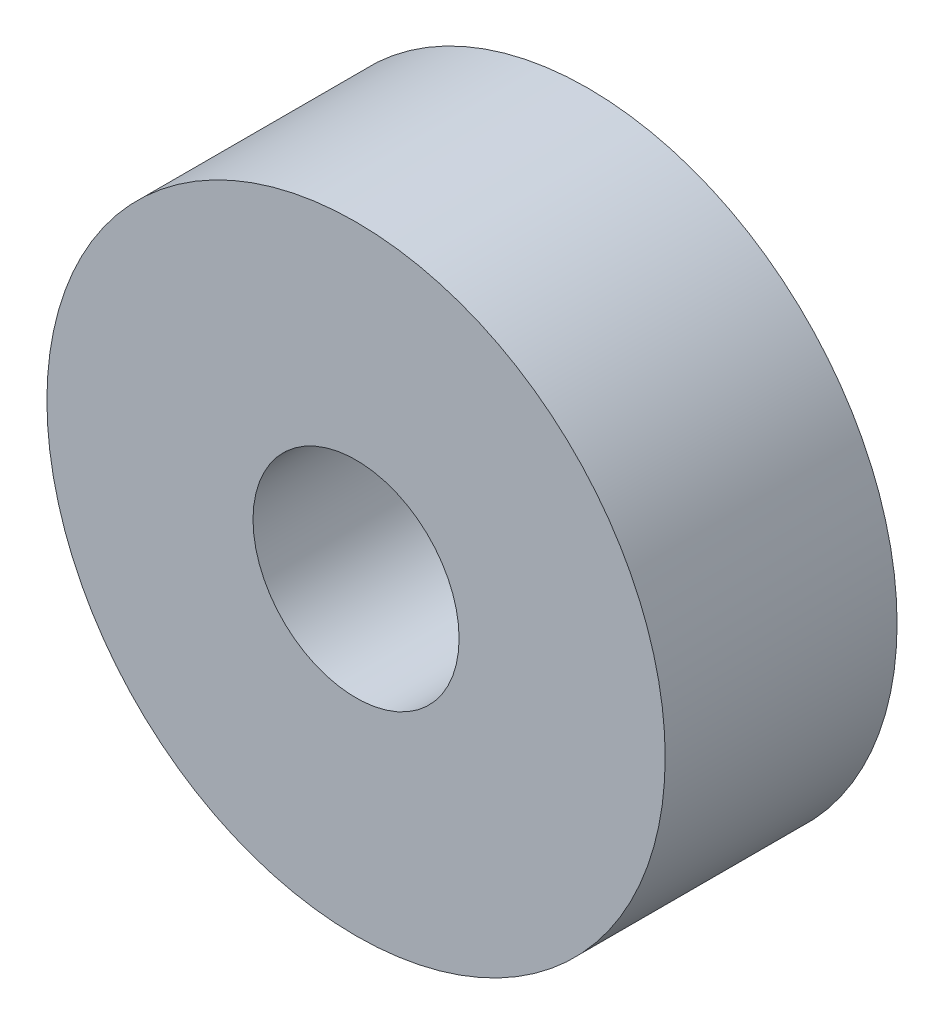
SolidWorks part; units mm, degrees
ref_plane "Front Plane" through (0, 0, 0) normal (0, 0, 1) x (1, 0, 0)
ref_plane "Top Plane" through (0, 0, 0) normal (0, 1, 0) x (1, 0, 0)
ref_plane "Right Plane" through (0, 0, 0) normal (1, 0, 0) x (0, 0, -1)
sketch "Sketch1" plane through (0, 0, 0) normal (0, 0, 1) x (1, 0, 0)
  circle A0 centre (0, 0) radius 3.175
  circle A1 centre (0, 0) radius 9.525
  dimension "D1" = 19.05
  dimension "D2" = 6.35
extrude "Boss-Extrude1" add sketch "Sketch1" along normal blind 7.145
